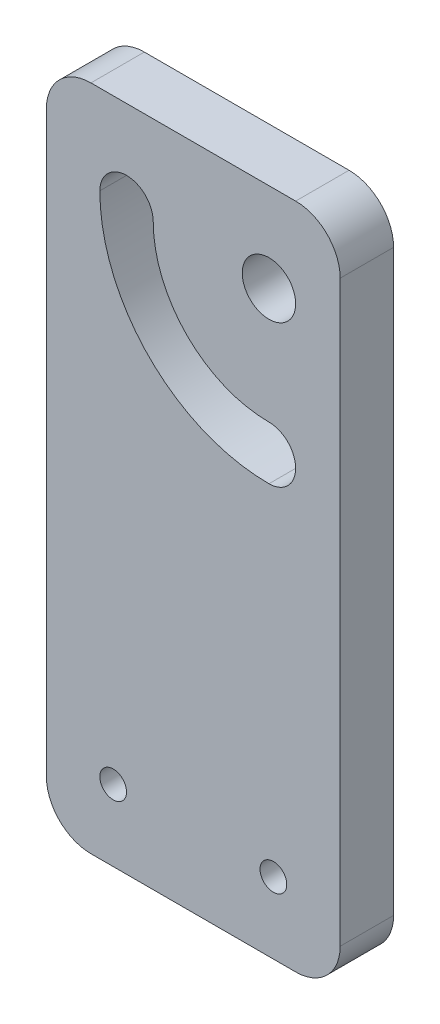
SolidWorks part; units mm, degrees
other "Marcação1"
sketch "Esboço5" plane through (0, 50, 68.25) normal (-0.797, 0.1637, 0.5813) x (0.5636, -0.1442, 0.8134)
material "Nylon - impressão"
ref_plane "Plano frontal" through (0, 0, 0) normal (0, 0, 1) x (1, 0, 0)
ref_plane "Plano superior" through (0, 0, 0) normal (0, 1, 0) x (1, 0, 0)
ref_plane "Plano direito" through (0, 0, 0) normal (1, 0, 0) x (0, 0, -1)
sketch "Esboço1" plane through (0, 0, 0) normal (0, 0, 1) x (1, 0, 0)
  line L1 (5, 50) -> (28, 50)
  line L4 (25, 40) -> (25, 37) construction
  line L8 (33, 45) -> (33, -20)
  line L9 (0, 45) -> (0, -20)
  line L11 (5, -25) -> (28, -25)
  circle A0 centre (25, 40) radius 3
  arc A2 (25, 24) -> (9, 40) centre (25, 40) cw construction
  arc A3 (6, 40) -> (25, 21) centre (25, 40) ccw
  arc A4 (12, 40) -> (25, 27) centre (25, 40) ccw
  arc A5 (12, 40) -> (6, 40) centre (9, 40) ccw
  arc A6 (25, 21) -> (25, 27) centre (25, 24) ccw
  circle A7 centre (25.5, -17) radius 1.5
  circle A8 centre (7.5, -17) radius 1.5
  arc A10 (0, 45) -> (5, 50) centre (5, 45) cw
  arc A12 (28, 50) -> (33, 45) centre (28, 45) cw
  arc A13 (28, -25) -> (33, -20) centre (28, -20) ccw
  arc A14 (5, -25) -> (0, -20) centre (5, -20) cw
  point P8 (0, 0)
  point P10 (13.6863, 28.6863)
  point P25 (0, 50)
  point P31 (33, 50)
  dimension "D3" = 6
  dimension "D5" = 16
  dimension "D6" = 13
  dimension "D2" = 3
  dimension "D4" = 8
  dimension "D8" = 7.5
  dimension "D9" = 8
  dimension "D10" = 5
  dimension "D1" = 75
  dimension "D7" = 33
  dimension "D11" = 10
  dimension "D12" = 10
extrude "Ressalto-extrusão2" add sketch "Esboço1" along normal blind 6
